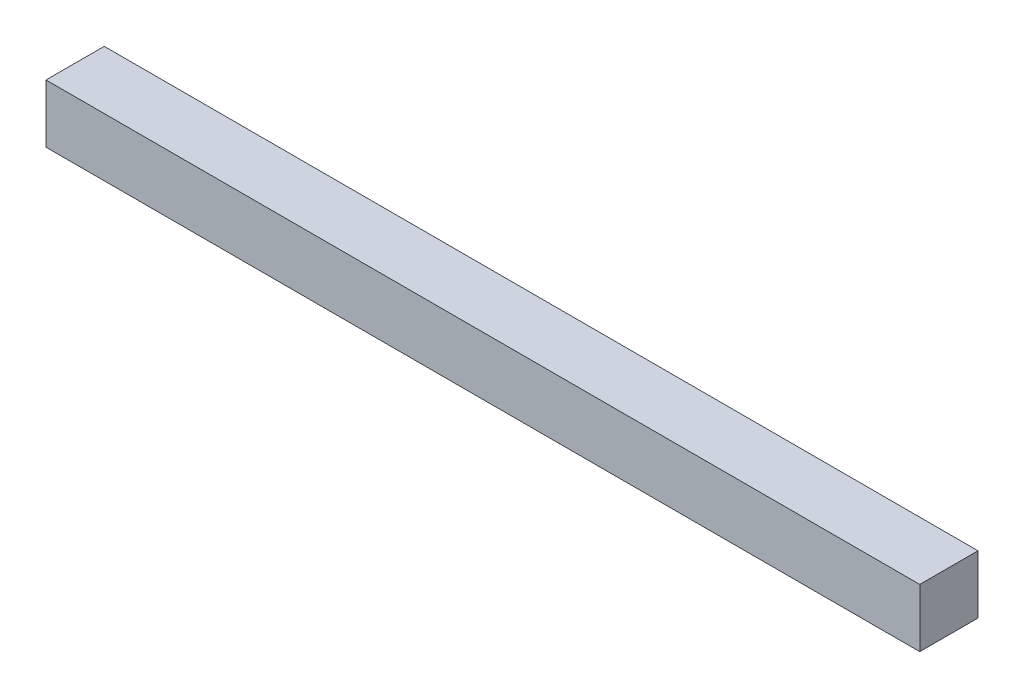
SolidWorks part; units mm, degrees
ref_plane "Front Plane" through (0, 0, 0) normal (0, 0, 1) x (1, 0, 0)
ref_plane "Top Plane" through (0, 0, 0) normal (0, 1, 0) x (1, 0, 0)
ref_plane "Right Plane" through (0, 0, 0) normal (1, 0, 0) x (0, 0, -1)
sketch "Sketch1" plane through (0, 0, 0) normal (0, 0, 1) x (1, 0, 0)
  line L1 (381, -25.4) -> (-381, -25.4)
  line L2 (381, -25.4) -> (381, 25.4)
  line L3 (381, 25.4) -> (-381, 25.4)
  line L4 (-381, -25.4) -> (-381, 25.4)
  line L5 (381, -25.4) -> (-381, 25.4) construction
  line L6 (381, 25.4) -> (-381, -25.4) construction
  point P0 (0, 0)
  dimension "D1" = 762
  dimension "D2" = 50.8
extrude "Boss-Extrude1" add sketch "Sketch1" along normal blind 50.8
